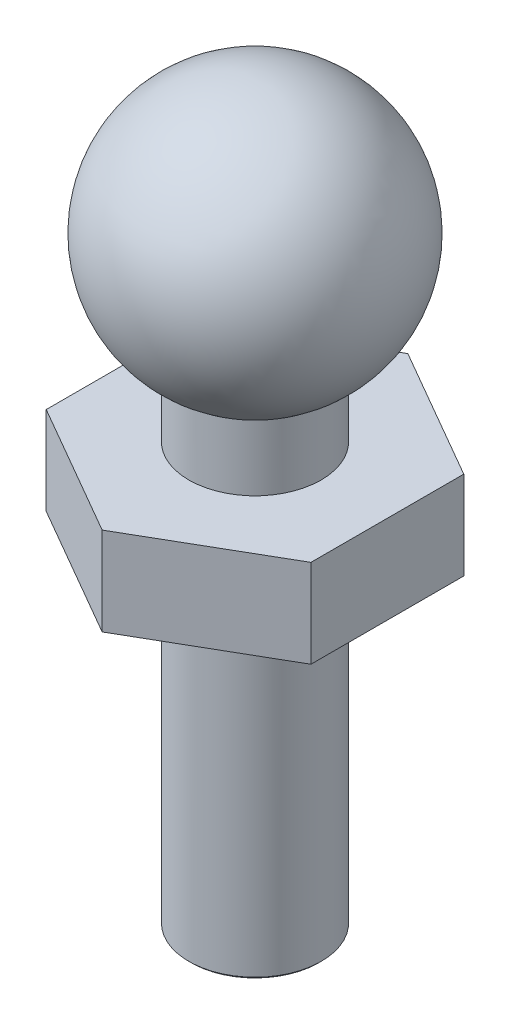
SolidWorks part; units mm, degrees
material "AISI 1045 Acero estirado en frío"
ref_plane "Front Plane" through (0, 0, 0) normal (0, 0, 1) x (1, 0, 0)
ref_plane "Top Plane" through (0, 0, 0) normal (0, 1, 0) x (1, 0, 0)
ref_plane "Right Plane" through (0, 0, 0) normal (1, 0, 0) x (0, 0, -1)
sketch "Sketch1" plane through (0, 0, 0) normal (0, 0, 1) x (1, 0, 0)
  line L0 (0, 0) -> (0, 16.5981) construction
  line L1 (0, 0) -> (1.5, 0)
  line L2 (1.5, 0) -> (1.5, 11)
  line L3 (0, 0) -> (0, 16.5981)
  arc A0 (0, 16.5981) -> (1.5, 11) centre (0, 13.5981) cw
  dimension "D1" = 11
  dimension "D3" = 3
  dimension "D2" = 1.5
revolve "Revolve1" add sketch "Sketch1" angle 360 about L0
sketch "Sketch2" plane through (0, 0, 0) normal (0, 0, 1) x (1, 0, 0)
  line L0 (-4.5696, 7.5) -> (7.3959, 7.5)
  dimension "D1" = 7.5
split line "Split Line1"
fillet "Fillet1" [suppressed] radius 0.5
chamfer "Chamfer1" distance 0.05 angle 45 1 edges at (0, 0, -1.5)
ref_plane "Plane1" through (0, 7.5, 0) normal (0, 1, 0) x (1, 0, 0)
sketch "Sketch3" plane through (0, 7.5, 0) normal (0, 1, 0) x (1, 0, 0)
  line L1 (3, 1.7321) -> (0, 3.4641)
  line L2 (0, 3.4641) -> (-3, 1.7321)
  line L3 (-3, 1.7321) -> (-3, -1.7321)
  line L4 (-3, -1.7321) -> (0, -3.4641)
  line L5 (0, -3.4641) -> (3, -1.7321)
  line L6 (3, -1.7321) -> (3, 1.7321)
  circle A0 centre (0, 0) radius 3 construction
  circle A1 centre (0, 0) radius 1.5 construction
  circle A2 centre (0, 0) radius 1.5
  dimension "D1" = 6
extrude "Boss-Extrude1" add sketch "Sketch3" along normal blind 2
